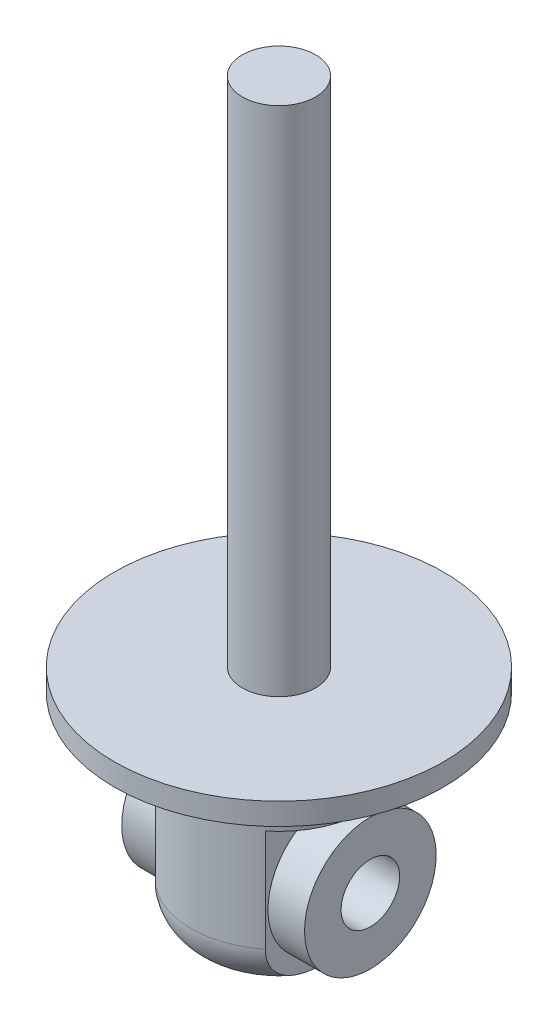
SolidWorks part; units mm, degrees
ref_plane "Front Plane" through (0, 0, 0) normal (0, 0, 1) x (1, 0, 0)
ref_plane "Top Plane" through (0, 0, 0) normal (0, 1, 0) x (1, 0, 0)
ref_plane "Right Plane" through (0, 0, 0) normal (1, 0, 0) x (0, 0, -1)
sketch "Sketch1" plane through (0, 0, 0) normal (0, 1, 0) x (1, 0, 0)
  circle A0 centre (0, 0) radius 225
  dimension "D1" = 450
extrude "Boss-Extrude1" add sketch "Sketch1" along normal blind 30
sketch "Sketch2" plane through (0, 30, 0) normal (0, 1, 0) x (1, 0, 0)
  circle A0 centre (0, 0) radius 50
  dimension "D1" = 100
extrude "Boss-Extrude2" add sketch "Sketch2" along normal blind 700
sketch "Sketch3" plane through (0, 0, 0) normal (0, -1, 0) x (1, 0, 0)
  circle A0 centre (0, 0) radius 120
  dimension "D1" = 240
extrude "Boss-Extrude3" add sketch "Sketch3" along normal blind 280
fillet "Fillet1" radius 60 1 edges at (0, -280, -120)
sketch "Sketch4" plane through (0, 0, 0) normal (0, 0, 1) x (1, 0, 0)
  line L0 (0, 0) -> (0, -280)
  line L1 (-60, -280) -> (60, -280) construction
  line L2 (-270.7, -280) -> (270.7, -280)
  line L3 (270.7, -280) -> (270.7, -80)
  line L4 (270.7, -80) -> (75, -80)
  line L5 (75, -80) -> (75, -280)
  line L6 (-270.7, -80) -> (-75, -80)
  line L7 (-270.7, -280) -> (-270.7, -80)
  line L8 (-75, -80) -> (-75, -280)
extrude "Cut-Extrude1" cut sketch "Sketch4" against normal through all both and the other way through all contours L4 L5 L2 L3 | L8 L6 L7 L2
sketch "Sketch5" plane through (75, 0, 0) normal (1, 0, 0) x (0, 0, -1)
  circle A0 centre (0, -175.3312) radius 40
  dimension "D1" = 80
extrude "Cut-Extrude2" cut sketch "Sketch5" against normal through all
sketch "Sketch7" plane through (75, 0, 0) normal (1, 0, 0) x (0, 0, -1)
  line L0 (-60, -280) -> (60, -280) construction
  point P1 (-80.7993, -114.1271)
  point P3 (0, -280)
sketch "Sketch6" plane through (0, 0, 0) normal (1, 0, 0) x (0, 0, -1)
  circle A0 centre (0, -175.3312) radius 90
  circle A1 centre (0, -175.3312) radius 40 construction
  circle A2 centre (0, -175.3312) radius 40
  dimension "D1" = 180
extrude "Boss-Extrude4" add sketch "Sketch6" along normal mid plane 250
scale "Scale1" scale about centroid uniform scaling yes scale factor 0.4
